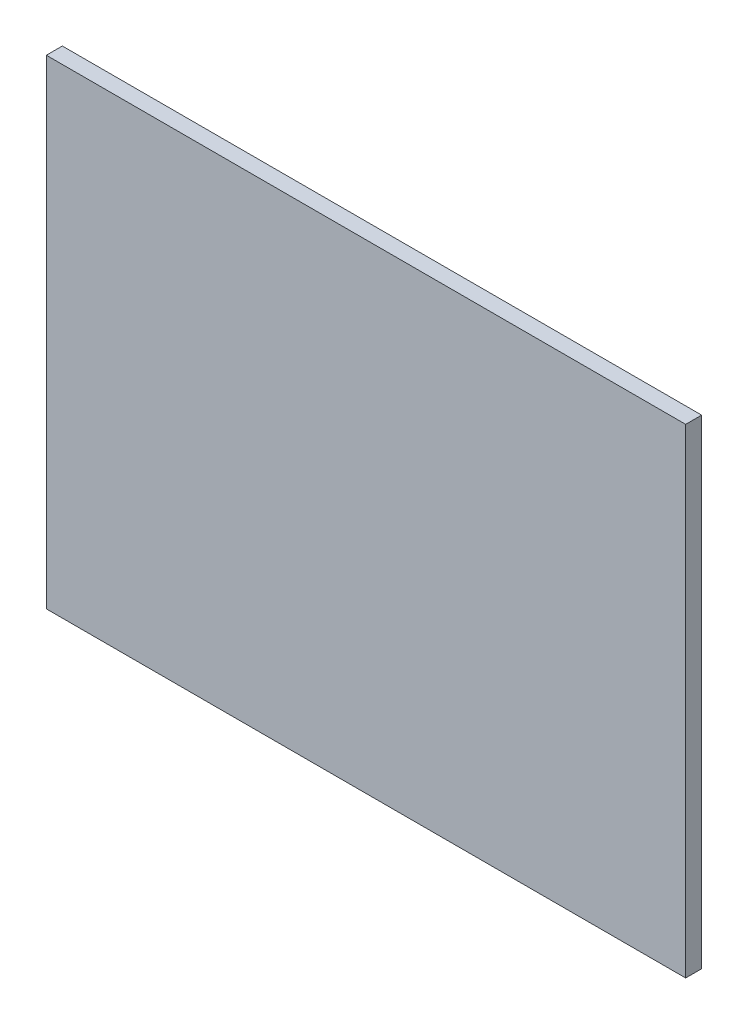
SolidWorks part; units mm, degrees
ref_plane "前视基准面" through (0, 0, 0) normal (0, 0, 1) x (1, 0, 0)
ref_plane "上视基准面" through (0, 0, 0) normal (0, 1, 0) x (1, 0, 0)
ref_plane "右视基准面" through (0, 0, 0) normal (1, 0, 0) x (0, 0, -1)
sketch "草图1" plane through (0, 0, 0) normal (0, 0, 1) x (1, 0, 0)
  line L0 (-56.5826, 23.7372) -> (-56.5826, -276.2628)
  line L1 (-56.5826, -276.2628) -> (343.4174, -276.2628)
  line L2 (343.4174, -276.2628) -> (343.4174, 23.7372)
  line L3 (343.4174, 23.7372) -> (-56.5826, 23.7372)
  dimension "D1" = 300
  dimension "D2" = 400
extrude "凸台-拉伸1" add sketch "草图1" along normal blind 10
